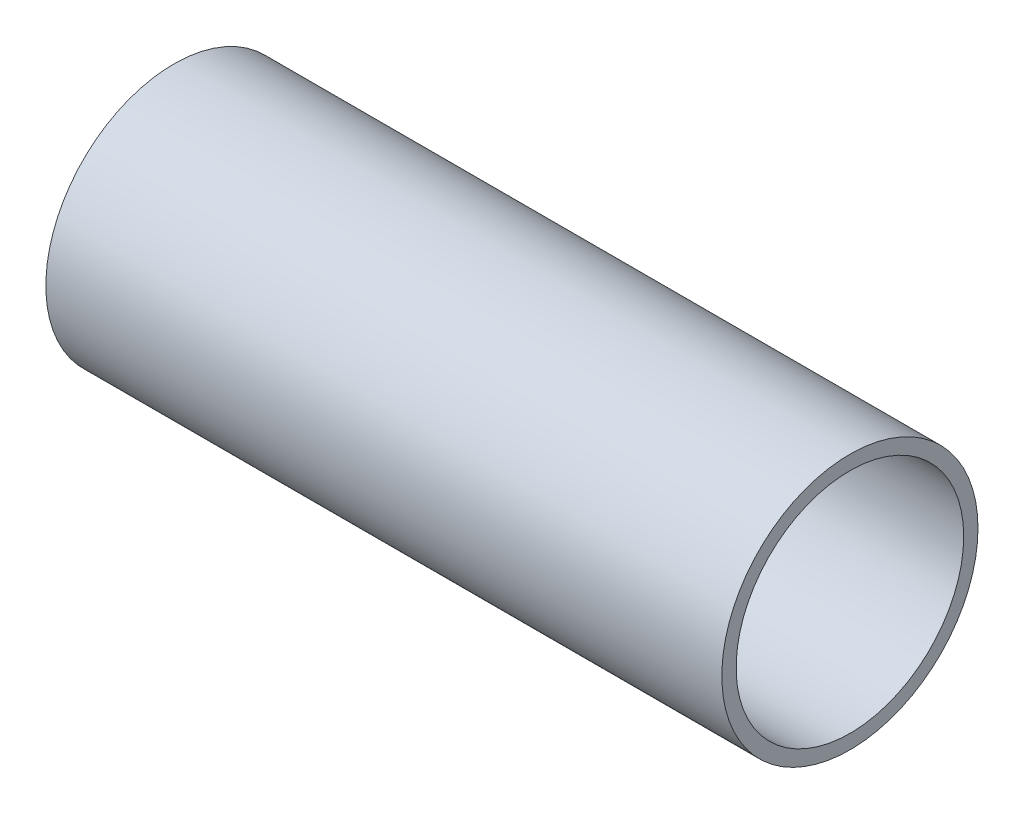
SolidWorks part; units mm, degrees
material "PVC Rigid"
ref_plane "Front Plane" through (0, 0, 0) normal (0, 0, 1) x (1, 0, 0)
ref_plane "Top Plane" through (0, 0, 0) normal (0, 1, 0) x (1, 0, 0)
ref_plane "Right Plane" through (0, 0, 0) normal (1, 0, 0) x (0, 0, -1)
sketch "Sketch1" plane through (0, 0, 0) normal (1, 0, 0) x (0, 0, -1)
  circle A0 centre (0, 0) radius 57.15
  circle A1 centre (0, 0) radius 50.7746
  dimension "D1" = 101.5492
  dimension "D2" = 114.3
extrude "Boss-Extrude1" add sketch "Sketch1" along normal blind 301.625
